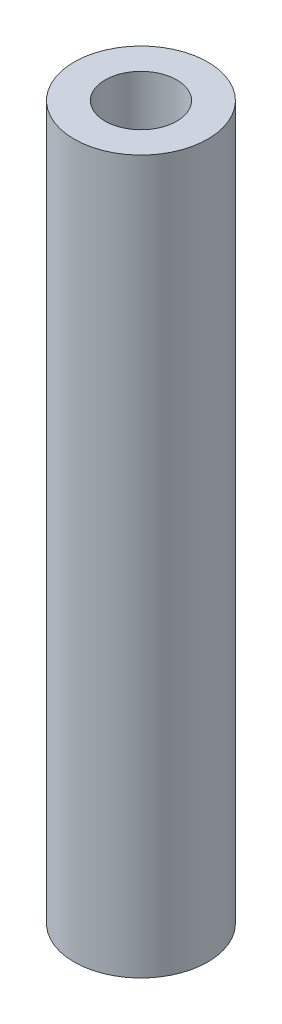
SolidWorks part; units mm, degrees
material "6061-T6 (SS)"
ref_plane "Front Plane" through (0, 0, 0) normal (0, 0, 1) x (1, 0, 0)
ref_plane "Top Plane" through (0, 0, 0) normal (0, 1, 0) x (1, 0, 0)
ref_plane "Right Plane" through (0, 0, 0) normal (1, 0, 0) x (0, 0, -1)
sketch "Sketch1" plane through (0, 0, 0) normal (0, 1, 0) x (1, 0, 0)
  circle A0 centre (0, 0) radius 4.7625
  circle A1 centre (0, 0) radius 2.5527
  dimension "D1" = 5.1054
  dimension "D2" = 9.525
extrude "Boss-Extrude1" add sketch "Sketch1" along normal mid plane 50.8
